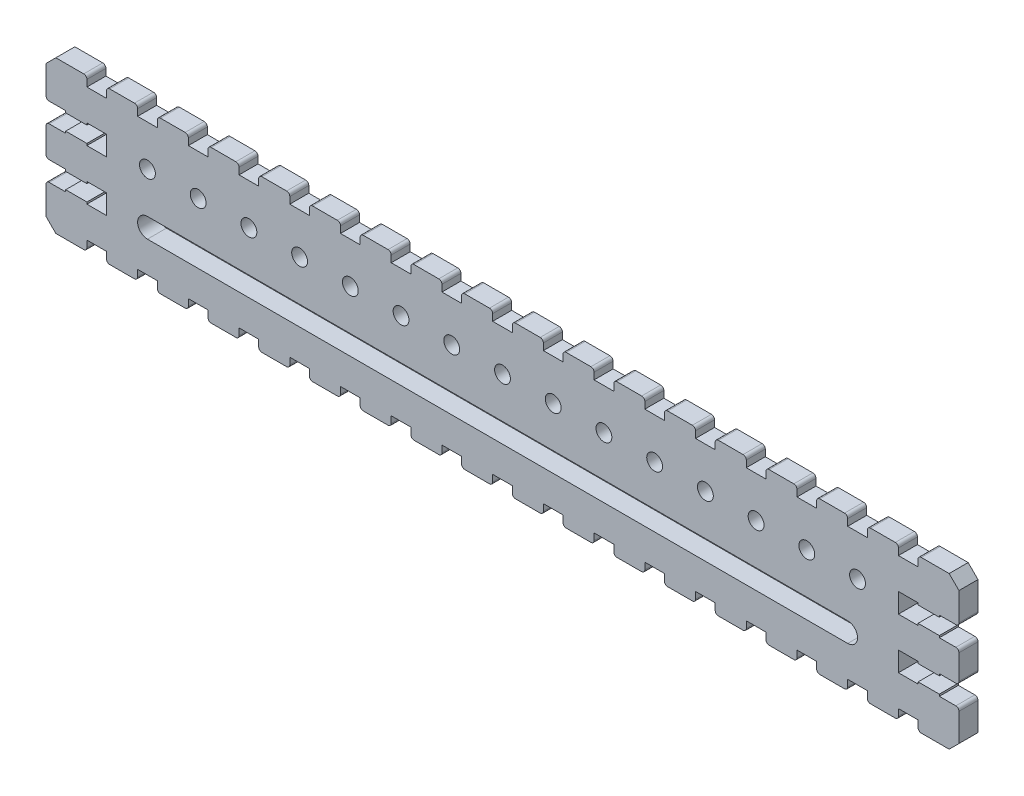
SolidWorks part; units mm, degrees
ref_plane "前视基准面" through (0, 0, 0) normal (0, 0, 1) x (1, 0, 0)
ref_plane "上视基准面" through (0, 0, 0) normal (0, 1, 0) x (1, 0, 0)
ref_plane "右视基准面" through (0, 0, 0) normal (1, 0, 0) x (0, 0, -1)
sketch "草图1" plane through (0, 0, 0) normal (0, 0, 1) x (1, 0, 0)
  line L0 (8.3412, 48.3798) -> (12.7412, 48.3798)
  line L1 (6.7912, 46.8298) -> (8.3412, 48.3798)
  line L2 (6.7912, 34.4298) -> (6.7912, 38.3298)
  line L3 (6.7912, 42.4298) -> (6.7912, 46.8298)
  line L4 (7.2912, 41.9298) -> (9.8912, 41.9298)
  line L5 (9.8912, 41.9298) -> (9.8912, 41.6298)
  line L6 (13.2412, 41.6298) -> (13.2412, 41.9298)
  line L7 (13.2412, 41.9298) -> (16.3412, 41.9298)
  line L8 (16.3412, 41.9298) -> (16.3412, 38.8298)
  line L9 (16.3412, 38.8298) -> (13.2412, 38.8298)
  line L10 (13.2412, 38.8298) -> (13.2412, 39.1298)
  line L11 (9.8912, 38.8298) -> (7.2912, 38.8298)
  line L12 (9.8912, 38.8298) -> (9.8912, 39.1298)
  line L13 (9.8912, 39.1298) -> (13.2412, 39.1298)
  line L14 (9.8912, 41.6298) -> (13.2412, 41.6298)
  line L15 (7.2912, 33.9298) -> (9.8912, 33.9298)
  line L16 (9.8912, 30.8298) -> (7.2912, 30.8298)
  line L17 (9.8912, 31.1298) -> (13.2412, 31.1298)
  line L18 (9.8912, 33.6298) -> (13.2412, 33.6298)
  line L19 (13.2412, 47.8798) -> (13.2412, 46.8298)
  line L20 (16.3412, 46.8298) -> (16.3412, 47.8798)
  line L21 (133.2412, 33.9298) -> (22.7912, 33.9298)
  line L22 (22.7912, 30.8298) -> (133.2412, 30.8298)
  line L23 (8.3412, 24.3798) -> (12.7412, 24.3798)
  line L24 (6.7912, 25.9298) -> (8.3412, 24.3798)
  line L25 (6.7912, 30.3298) -> (6.7912, 25.9298)
  line L26 (9.8912, 30.8298) -> (9.8912, 31.1298)
  line L27 (13.2412, 31.1298) -> (13.2412, 30.8298)
  line L28 (13.2412, 30.8298) -> (16.3412, 30.8298)
  line L29 (16.3412, 30.8298) -> (16.3412, 33.9298)
  line L30 (16.3412, 33.9298) -> (13.2412, 33.9298)
  line L31 (13.2412, 33.9298) -> (13.2412, 33.6298)
  line L32 (9.8912, 33.9298) -> (9.8912, 33.6298)
  line L33 (150.7912, 46.8298) -> (149.2412, 48.3798)
  line L34 (150.7912, 34.4298) -> (150.7912, 38.3298)
  line L35 (150.7912, 42.4298) -> (150.7912, 46.8298)
  line L36 (150.2912, 41.9298) -> (147.6912, 41.9298)
  line L37 (147.6912, 41.9298) -> (147.6912, 41.6298)
  line L38 (144.3412, 41.6298) -> (144.3412, 41.9298)
  line L39 (144.3412, 41.9298) -> (141.2412, 41.9298)
  line L40 (141.2412, 41.9298) -> (141.2412, 38.8298)
  line L41 (141.2412, 38.8298) -> (144.3412, 38.8298)
  line L42 (144.3412, 38.8298) -> (144.3412, 39.1298)
  line L43 (147.6912, 38.8298) -> (150.2912, 38.8298)
  line L44 (147.6912, 38.8298) -> (147.6912, 39.1298)
  line L45 (147.6912, 39.1298) -> (144.3412, 39.1298)
  line L46 (147.6912, 41.6298) -> (144.3412, 41.6298)
  line L47 (150.2912, 33.9298) -> (147.6912, 33.9298)
  line L48 (147.6912, 30.8298) -> (150.2912, 30.8298)
  line L49 (147.6912, 31.1298) -> (144.3412, 31.1298)
  line L50 (147.6912, 33.6298) -> (144.3412, 33.6298)
  line L51 (144.3412, 47.8798) -> (144.3412, 46.8298)
  line L52 (141.2412, 46.8298) -> (141.2412, 47.8798)
  line L53 (149.2412, 24.3798) -> (144.8412, 24.3798)
  line L54 (150.7912, 25.9298) -> (149.2412, 24.3798)
  line L55 (150.7912, 30.3298) -> (150.7912, 25.9298)
  line L56 (147.6912, 30.8298) -> (147.6912, 31.1298)
  line L57 (144.3412, 31.1298) -> (144.3412, 30.8298)
  line L58 (144.3412, 30.8298) -> (141.2412, 30.8298)
  line L59 (141.2412, 30.8298) -> (141.2412, 33.9298)
  line L60 (141.2412, 33.9298) -> (144.3412, 33.9298)
  line L61 (144.3412, 33.9298) -> (144.3412, 33.6298)
  line L62 (147.6912, 33.9298) -> (147.6912, 33.6298)
  line L63 (144.3412, 24.8798) -> (144.3412, 25.9298)
  line L64 (144.3412, 25.9298) -> (141.2412, 25.9298)
  line L65 (141.2412, 25.9298) -> (141.2412, 24.8798)
  line L66 (140.7412, 24.3798) -> (136.8412, 24.3798)
  line L67 (13.2412, 24.8798) -> (13.2412, 25.9298)
  line L68 (13.2412, 25.9298) -> (16.3412, 25.9298)
  line L69 (16.3412, 25.9298) -> (16.3412, 24.8798)
  line L70 (16.8412, 24.3798) -> (20.7412, 24.3798)
  line L71 (21.2412, 24.8798) -> (21.2412, 25.9298)
  line L72 (21.2412, 25.9298) -> (24.3412, 25.9298)
  line L73 (24.3412, 25.9298) -> (24.3412, 24.8798)
  line L74 (24.8412, 24.3798) -> (28.7412, 24.3798)
  line L75 (29.2412, 24.8798) -> (29.2412, 25.9298)
  line L76 (29.2412, 25.9298) -> (32.3412, 25.9298)
  line L77 (32.3412, 25.9298) -> (32.3412, 24.8798)
  line L78 (32.8412, 24.3798) -> (36.7412, 24.3798)
  line L79 (37.2412, 24.8798) -> (37.2412, 25.9298)
  line L80 (37.2412, 25.9298) -> (40.3412, 25.9298)
  line L81 (40.3412, 25.9298) -> (40.3412, 24.8798)
  line L82 (40.8412, 24.3798) -> (44.7412, 24.3798)
  line L83 (45.2412, 24.8798) -> (45.2412, 25.9298)
  line L84 (45.2412, 25.9298) -> (48.3412, 25.9298)
  line L85 (48.3412, 25.9298) -> (48.3412, 24.8798)
  line L86 (48.8412, 24.3798) -> (52.7412, 24.3798)
  line L87 (53.2412, 24.8798) -> (53.2412, 25.9298)
  line L88 (53.2412, 25.9298) -> (56.3412, 25.9298)
  line L89 (56.3412, 25.9298) -> (56.3412, 24.8798)
  line L90 (56.8412, 24.3798) -> (60.7412, 24.3798)
  line L91 (61.2412, 24.8798) -> (61.2412, 25.9298)
  line L92 (61.2412, 25.9298) -> (64.3412, 25.9298)
  line L93 (64.3412, 25.9298) -> (64.3412, 24.8798)
  line L94 (64.8412, 24.3798) -> (68.7412, 24.3798)
  line L95 (69.2412, 24.8798) -> (69.2412, 25.9298)
  line L96 (69.2412, 25.9298) -> (72.3412, 25.9298)
  line L97 (72.3412, 25.9298) -> (72.3412, 24.8798)
  line L98 (72.8412, 24.3798) -> (76.7412, 24.3798)
  line L99 (77.2412, 24.8798) -> (77.2412, 25.9298)
  line L100 (77.2412, 25.9298) -> (80.3412, 25.9298)
  line L101 (80.3412, 25.9298) -> (80.3412, 24.8798)
  line L102 (80.8412, 24.3798) -> (84.7412, 24.3798)
  line L103 (85.2412, 24.8798) -> (85.2412, 25.9298)
  line L104 (85.2412, 25.9298) -> (88.3412, 25.9298)
  line L105 (88.3412, 25.9298) -> (88.3412, 24.8798)
  line L106 (88.8412, 24.3798) -> (92.7412, 24.3798)
  line L107 (93.2412, 24.8798) -> (93.2412, 25.9298)
  line L108 (93.2412, 25.9298) -> (96.3412, 25.9298)
  line L109 (96.3412, 25.9298) -> (96.3412, 24.8798)
  line L110 (96.8412, 24.3798) -> (100.7412, 24.3798)
  line L111 (101.2412, 24.8798) -> (101.2412, 25.9298)
  line L112 (101.2412, 25.9298) -> (104.3412, 25.9298)
  line L113 (104.3412, 25.9298) -> (104.3412, 24.8798)
  line L114 (104.8412, 24.3798) -> (108.7412, 24.3798)
  line L115 (109.2412, 24.8798) -> (109.2412, 25.9298)
  line L116 (109.2412, 25.9298) -> (112.3412, 25.9298)
  line L117 (112.3412, 25.9298) -> (112.3412, 24.8798)
  line L118 (112.8412, 24.3798) -> (116.7412, 24.3798)
  line L119 (117.2412, 24.8798) -> (117.2412, 25.9298)
  line L120 (117.2412, 25.9298) -> (120.3412, 25.9298)
  line L121 (120.3412, 25.9298) -> (120.3412, 24.8798)
  line L122 (120.8412, 24.3798) -> (124.7412, 24.3798)
  line L123 (125.2412, 24.8798) -> (125.2412, 25.9298)
  line L124 (125.2412, 25.9298) -> (128.3412, 25.9298)
  line L125 (128.3412, 25.9298) -> (128.3412, 24.8798)
  line L126 (128.8412, 24.3798) -> (132.7412, 24.3798)
  line L127 (133.2412, 24.8798) -> (133.2412, 25.9298)
  line L128 (133.2412, 25.9298) -> (136.3412, 25.9298)
  line L129 (136.3412, 25.9298) -> (136.3412, 24.8798)
  line L130 (149.2412, 48.3798) -> (144.8412, 48.3798)
  line L131 (144.3412, 46.8298) -> (141.2412, 46.8298)
  line L132 (13.2412, 46.8298) -> (16.3412, 46.8298)
  line L133 (16.8412, 48.3798) -> (20.7412, 48.3798)
  line L134 (21.2412, 47.8798) -> (21.2412, 46.8298)
  line L135 (21.2412, 46.8298) -> (24.3412, 46.8298)
  line L136 (24.3412, 46.8298) -> (24.3412, 47.8798)
  line L137 (24.8412, 48.3798) -> (28.7412, 48.3798)
  line L138 (29.2412, 47.8798) -> (29.2412, 46.8298)
  line L139 (29.2412, 46.8298) -> (32.3412, 46.8298)
  line L140 (32.3412, 46.8298) -> (32.3412, 47.8798)
  line L141 (32.8412, 48.3798) -> (36.7412, 48.3798)
  line L142 (37.2412, 47.8798) -> (37.2412, 46.8298)
  line L143 (37.2412, 46.8298) -> (40.3412, 46.8298)
  line L144 (40.3412, 46.8298) -> (40.3412, 47.8798)
  line L145 (40.8412, 48.3798) -> (44.7412, 48.3798)
  line L146 (45.2412, 47.8798) -> (45.2412, 46.8298)
  line L147 (45.2412, 46.8298) -> (48.3412, 46.8298)
  line L148 (48.3412, 46.8298) -> (48.3412, 47.8798)
  line L149 (48.8412, 48.3798) -> (52.7412, 48.3798)
  line L150 (53.2412, 47.8798) -> (53.2412, 46.8298)
  line L151 (53.2412, 46.8298) -> (56.3412, 46.8298)
  line L152 (56.3412, 46.8298) -> (56.3412, 47.8798)
  line L153 (56.8412, 48.3798) -> (60.7412, 48.3798)
  line L154 (61.2412, 47.8798) -> (61.2412, 46.8298)
  line L155 (61.2412, 46.8298) -> (64.3412, 46.8298)
  line L156 (64.3412, 46.8298) -> (64.3412, 47.8798)
  line L157 (64.8412, 48.3798) -> (68.7412, 48.3798)
  line L158 (69.2412, 47.8798) -> (69.2412, 46.8298)
  line L159 (69.2412, 46.8298) -> (72.3412, 46.8298)
  line L160 (72.3412, 46.8298) -> (72.3412, 47.8798)
  line L161 (72.8412, 48.3798) -> (76.7412, 48.3798)
  line L162 (77.2412, 47.8798) -> (77.2412, 46.8298)
  line L163 (77.2412, 46.8298) -> (80.3412, 46.8298)
  line L164 (80.3412, 46.8298) -> (80.3412, 47.8798)
  line L165 (80.8412, 48.3798) -> (84.7412, 48.3798)
  line L166 (85.2412, 47.8798) -> (85.2412, 46.8298)
  line L167 (85.2412, 46.8298) -> (88.3412, 46.8298)
  line L168 (88.3412, 46.8298) -> (88.3412, 47.8798)
  line L169 (88.8412, 48.3798) -> (92.7412, 48.3798)
  line L170 (93.2412, 47.8798) -> (93.2412, 46.8298)
  line L171 (93.2412, 46.8298) -> (96.3412, 46.8298)
  line L172 (96.3412, 46.8298) -> (96.3412, 47.8798)
  line L173 (96.8412, 48.3798) -> (100.7412, 48.3798)
  line L174 (101.2412, 47.8798) -> (101.2412, 46.8298)
  line L175 (101.2412, 46.8298) -> (104.3412, 46.8298)
  line L176 (104.3412, 46.8298) -> (104.3412, 47.8798)
  line L177 (104.8412, 48.3798) -> (108.7412, 48.3798)
  line L178 (109.2412, 47.8798) -> (109.2412, 46.8298)
  line L179 (109.2412, 46.8298) -> (112.3412, 46.8298)
  line L180 (112.3412, 46.8298) -> (112.3412, 47.8798)
  line L181 (112.8412, 48.3798) -> (116.7412, 48.3798)
  line L182 (117.2412, 47.8798) -> (117.2412, 46.8298)
  line L183 (117.2412, 46.8298) -> (120.3412, 46.8298)
  line L184 (120.3412, 46.8298) -> (120.3412, 47.8798)
  line L185 (120.8412, 48.3798) -> (124.7412, 48.3798)
  line L186 (125.2412, 47.8798) -> (125.2412, 46.8298)
  line L187 (125.2412, 46.8298) -> (128.3412, 46.8298)
  line L188 (128.3412, 46.8298) -> (128.3412, 47.8798)
  line L189 (128.8412, 48.3798) -> (132.7412, 48.3798)
  line L190 (133.2412, 47.8798) -> (133.2412, 46.8298)
  line L191 (133.2412, 46.8298) -> (136.3412, 46.8298)
  line L192 (136.3412, 46.8298) -> (136.3412, 47.8798)
  line L193 (136.8412, 48.3798) -> (140.7412, 48.3798)
  arc A0 (7.2912, 38.8298) -> (6.7912, 38.3298) centre (7.2912, 38.3298) ccw
  arc A1 (6.7912, 42.4298) -> (7.2912, 41.9298) centre (7.2912, 42.4298) ccw
  arc A2 (13.2412, 47.8798) -> (12.7412, 48.3798) centre (12.7412, 47.8798) ccw
  arc A3 (22.7912, 33.9298) -> (22.7912, 30.8298) centre (22.7912, 32.3798) ccw
  arc A4 (133.2412, 30.8298) -> (133.2412, 33.9298) centre (133.2412, 32.3798) ccw
  arc A5 (6.7912, 34.4298) -> (7.2912, 33.9298) centre (7.2912, 34.4298) ccw
  arc A6 (7.2912, 30.8298) -> (6.7912, 30.3298) centre (7.2912, 30.3298) ccw
  arc A7 (150.7912, 38.3298) -> (150.2912, 38.8298) centre (150.2912, 38.3298) ccw
  arc A8 (150.2912, 41.9298) -> (150.7912, 42.4298) centre (150.2912, 42.4298) ccw
  arc A9 (150.2912, 33.9298) -> (150.7912, 34.4298) centre (150.2912, 34.4298) ccw
  arc A10 (150.7912, 30.3298) -> (150.2912, 30.8298) centre (150.2912, 30.3298) ccw
  arc A11 (144.3412, 24.8798) -> (144.8412, 24.3798) centre (144.8412, 24.8798) ccw
  arc A12 (140.7412, 24.3798) -> (141.2412, 24.8798) centre (140.7412, 24.8798) ccw
  arc A13 (12.7412, 24.3798) -> (13.2412, 24.8798) centre (12.7412, 24.8798) ccw
  arc A14 (16.3412, 24.8798) -> (16.8412, 24.3798) centre (16.8412, 24.8798) ccw
  arc A15 (20.7412, 24.3798) -> (21.2412, 24.8798) centre (20.7412, 24.8798) ccw
  arc A16 (24.3412, 24.8798) -> (24.8412, 24.3798) centre (24.8412, 24.8798) ccw
  arc A17 (28.7412, 24.3798) -> (29.2412, 24.8798) centre (28.7412, 24.8798) ccw
  arc A18 (32.3412, 24.8798) -> (32.8412, 24.3798) centre (32.8412, 24.8798) ccw
  arc A19 (36.7412, 24.3798) -> (37.2412, 24.8798) centre (36.7412, 24.8798) ccw
  arc A20 (40.3412, 24.8798) -> (40.8412, 24.3798) centre (40.8412, 24.8798) ccw
  arc A21 (44.7412, 24.3798) -> (45.2412, 24.8798) centre (44.7412, 24.8798) ccw
  arc A22 (48.3412, 24.8798) -> (48.8412, 24.3798) centre (48.8412, 24.8798) ccw
  arc A23 (52.7412, 24.3798) -> (53.2412, 24.8798) centre (52.7412, 24.8798) ccw
  arc A24 (56.3412, 24.8798) -> (56.8412, 24.3798) centre (56.8412, 24.8798) ccw
  arc A25 (60.7412, 24.3798) -> (61.2412, 24.8798) centre (60.7412, 24.8798) ccw
  arc A26 (64.3412, 24.8798) -> (64.8412, 24.3798) centre (64.8412, 24.8798) ccw
  arc A27 (68.7412, 24.3798) -> (69.2412, 24.8798) centre (68.7412, 24.8798) ccw
  arc A28 (72.3412, 24.8798) -> (72.8412, 24.3798) centre (72.8412, 24.8798) ccw
  arc A29 (76.7412, 24.3798) -> (77.2412, 24.8798) centre (76.7412, 24.8798) ccw
  arc A30 (80.3412, 24.8798) -> (80.8412, 24.3798) centre (80.8412, 24.8798) ccw
  arc A31 (84.7412, 24.3798) -> (85.2412, 24.8798) centre (84.7412, 24.8798) ccw
  arc A32 (88.3412, 24.8798) -> (88.8412, 24.3798) centre (88.8412, 24.8798) ccw
  arc A33 (92.7412, 24.3798) -> (93.2412, 24.8798) centre (92.7412, 24.8798) ccw
  arc A34 (96.3412, 24.8798) -> (96.8412, 24.3798) centre (96.8412, 24.8798) ccw
  arc A35 (100.7412, 24.3798) -> (101.2412, 24.8798) centre (100.7412, 24.8798) ccw
  arc A36 (104.3412, 24.8798) -> (104.8412, 24.3798) centre (104.8412, 24.8798) ccw
  arc A37 (108.7412, 24.3798) -> (109.2412, 24.8798) centre (108.7412, 24.8798) ccw
  arc A38 (112.3412, 24.8798) -> (112.8412, 24.3798) centre (112.8412, 24.8798) ccw
  arc A39 (116.7412, 24.3798) -> (117.2412, 24.8798) centre (116.7412, 24.8798) ccw
  arc A40 (120.3412, 24.8798) -> (120.8412, 24.3798) centre (120.8412, 24.8798) ccw
  arc A41 (124.7412, 24.3798) -> (125.2412, 24.8798) centre (124.7412, 24.8798) ccw
  arc A42 (128.3412, 24.8798) -> (128.8412, 24.3798) centre (128.8412, 24.8798) ccw
  arc A43 (132.7412, 24.3798) -> (133.2412, 24.8798) centre (132.7412, 24.8798) ccw
  arc A44 (136.3412, 24.8798) -> (136.8412, 24.3798) centre (136.8412, 24.8798) ccw
  arc A45 (144.8412, 48.3798) -> (144.3412, 47.8798) centre (144.8412, 47.8798) ccw
  arc A46 (141.2412, 47.8798) -> (140.7412, 48.3798) centre (140.7412, 47.8798) ccw
  arc A47 (16.8412, 48.3798) -> (16.3412, 47.8798) centre (16.8412, 47.8798) ccw
  arc A48 (21.2412, 47.8798) -> (20.7412, 48.3798) centre (20.7412, 47.8798) ccw
  arc A49 (24.8412, 48.3798) -> (24.3412, 47.8798) centre (24.8412, 47.8798) ccw
  arc A50 (29.2412, 47.8798) -> (28.7412, 48.3798) centre (28.7412, 47.8798) ccw
  arc A51 (32.8412, 48.3798) -> (32.3412, 47.8798) centre (32.8412, 47.8798) ccw
  arc A52 (37.2412, 47.8798) -> (36.7412, 48.3798) centre (36.7412, 47.8798) ccw
  arc A53 (40.8412, 48.3798) -> (40.3412, 47.8798) centre (40.8412, 47.8798) ccw
  arc A54 (45.2412, 47.8798) -> (44.7412, 48.3798) centre (44.7412, 47.8798) ccw
  arc A55 (48.8412, 48.3798) -> (48.3412, 47.8798) centre (48.8412, 47.8798) ccw
  arc A56 (53.2412, 47.8798) -> (52.7412, 48.3798) centre (52.7412, 47.8798) ccw
  arc A57 (56.8412, 48.3798) -> (56.3412, 47.8798) centre (56.8412, 47.8798) ccw
  arc A58 (61.2412, 47.8798) -> (60.7412, 48.3798) centre (60.7412, 47.8798) ccw
  arc A59 (64.8412, 48.3798) -> (64.3412, 47.8798) centre (64.8412, 47.8798) ccw
  arc A60 (69.2412, 47.8798) -> (68.7412, 48.3798) centre (68.7412, 47.8798) ccw
  arc A61 (72.8412, 48.3798) -> (72.3412, 47.8798) centre (72.8412, 47.8798) ccw
  arc A62 (77.2412, 47.8798) -> (76.7412, 48.3798) centre (76.7412, 47.8798) ccw
  arc A63 (80.8412, 48.3798) -> (80.3412, 47.8798) centre (80.8412, 47.8798) ccw
  arc A64 (85.2412, 47.8798) -> (84.7412, 48.3798) centre (84.7412, 47.8798) ccw
  arc A65 (88.8412, 48.3798) -> (88.3412, 47.8798) centre (88.8412, 47.8798) ccw
  arc A66 (93.2412, 47.8798) -> (92.7412, 48.3798) centre (92.7412, 47.8798) ccw
  arc A67 (96.8412, 48.3798) -> (96.3412, 47.8798) centre (96.8412, 47.8798) ccw
  arc A68 (101.2412, 47.8798) -> (100.7412, 48.3798) centre (100.7412, 47.8798) ccw
  arc A69 (104.8412, 48.3798) -> (104.3412, 47.8798) centre (104.8412, 47.8798) ccw
  arc A70 (109.2412, 47.8798) -> (108.7412, 48.3798) centre (108.7412, 47.8798) ccw
  arc A71 (112.8412, 48.3798) -> (112.3412, 47.8798) centre (112.8412, 47.8798) ccw
  arc A72 (117.2412, 47.8798) -> (116.7412, 48.3798) centre (116.7412, 47.8798) ccw
  arc A73 (120.8412, 48.3798) -> (120.3412, 47.8798) centre (120.8412, 47.8798) ccw
  arc A74 (125.2412, 47.8798) -> (124.7412, 48.3798) centre (124.7412, 47.8798) ccw
  arc A75 (128.8412, 48.3798) -> (128.3412, 47.8798) centre (128.8412, 47.8798) ccw
  arc A76 (133.2412, 47.8798) -> (132.7412, 48.3798) centre (132.7412, 47.8798) ccw
  arc A77 (136.8412, 48.3798) -> (136.3412, 47.8798) centre (136.8412, 47.8798) ccw
  circle A78 centre (22.7912, 40.3798) radius 1.25
  circle A79 centre (30.7912, 40.3798) radius 1.25
  circle A80 centre (38.7912, 40.3798) radius 1.25
  circle A81 centre (46.7912, 40.3798) radius 1.25
  circle A82 centre (54.7912, 40.3798) radius 1.25
  circle A83 centre (62.7912, 40.3798) radius 1.25
  circle A84 centre (70.7912, 40.3798) radius 1.25
  circle A85 centre (78.7912, 40.3798) radius 1.25
  circle A86 centre (86.7912, 40.3798) radius 1.25
  circle A87 centre (94.7912, 40.3798) radius 1.25
  circle A88 centre (102.7912, 40.3798) radius 1.25
  circle A89 centre (110.7912, 40.3798) radius 1.25
  circle A90 centre (118.7912, 40.3798) radius 1.25
  circle A91 centre (126.7912, 40.3798) radius 1.25
  circle A92 centre (134.7912, 40.3798) radius 1.25
extrude "凸台-拉伸1" add sketch "草图1" along normal blind 3
